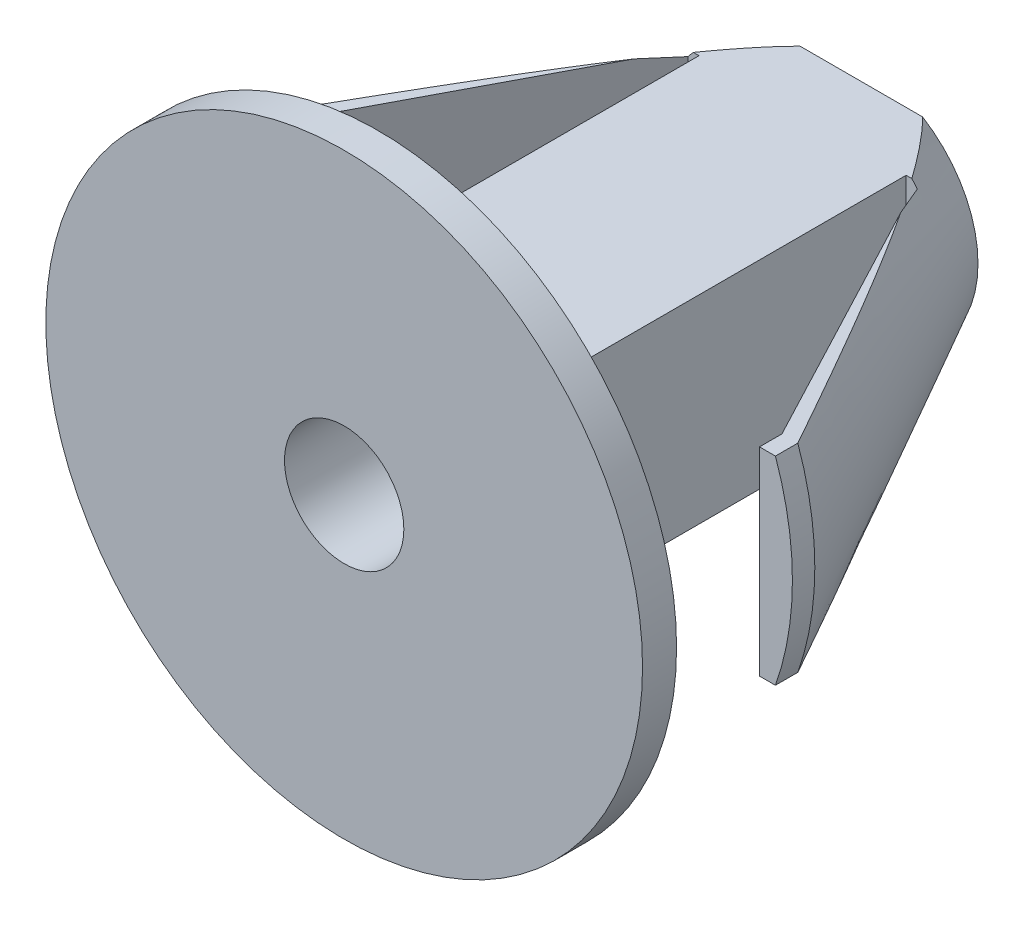
SolidWorks part; units mm, degrees
ref_plane "Front Plane" through (0, 0, 0) normal (0, 0, 1) x (1, 0, 0)
ref_plane "Top Plane" through (0, 0, 0) normal (0, 1, 0) x (1, 0, 0)
ref_plane "Right Plane" through (0, 0, 0) normal (1, 0, 0) x (0, 0, -1)
sketch "Sketch2" plane through (0, 0, 0) normal (0, 1, 0) x (1, 0, 0)
  line L0 (0, 5.1698) -> (-2.9321, 5.1698)
  line L1 (-2.9321, 5.1698) -> (-7.5, -3.4997)
  line L2 (-7.5, -3.4997) -> (-7.5, -7.8302)
  line L3 (-7.5, -7.8302) -> (0, -7.8302)
  line L4 (0, -7.8302) -> (0, 5.1698)
  dimension "D1" = 7.5
  dimension "D2" = 13
revolve "Revolve1" add sketch "Sketch2" angle 360 about L4
sketch "Sketch3" plane through (0, 0, 0) normal (0, 1, 0) x (1, 0, 0)
  line L0 (-7.6964, -4.0631) -> (-4.4271, -4.0631)
  line L1 (-4.4271, -4.0631) -> (-4.4271, -6.9748)
  line L2 (-4.4271, -6.9748) -> (-8.4456, -6.9748)
  line L3 (-8.4456, -6.9748) -> (-7.6964, -4.0631)
  line L4 (0, 0) -> (0, -8.4221) construction
  line L5 (8.4456, -6.9748) -> (7.6964, -4.0631)
  line L6 (4.4271, -6.9748) -> (8.4456, -6.9748)
  line L7 (4.4271, -4.0631) -> (4.4271, -6.9748)
  line L8 (7.6964, -4.0631) -> (4.4271, -4.0631)
extrude "Cut-Extrude1" cut sketch "Sketch3" against normal through all both and the other way through all
sketch "Sketch4" plane through (0, 0, 0) normal (0, 1, 0) x (1, 0, 0)
  line L0 (-6.673, -4.0631) -> (-6.673, -3.4997)
  line L1 (-7.5, -4.0631) -> (-4.4271, -4.0631) construction
  line L2 (7.5, -3.4997) -> (-7.5, -3.4997) construction
  line L3 (-6.673, -3.4997) -> (-2.8837, 3.6921)
  line L4 (-2.6031, 3.6921) -> (-2.6031, -4.0631)
  line L6 (-2.9321, 5.1698) -> (-7.5, -3.4997) construction
  line L7 (-2.8837, 3.6921) -> (-2.6031, 3.6921)
  line L8 (0, 5.6234) -> (0, -0.5002) construction
  line L14 (-6.673, -4.0631) -> (-6.673, -6.9748)
  line L15 (-4.4271, -6.9748) -> (-7.5, -6.9748) construction
  line L16 (-6.673, -6.9748) -> (-2.6031, -6.9748)
  line L17 (-2.6031, -6.9748) -> (-2.6031, -4.0631)
  line L18 (2.6031, -6.9748) -> (2.6031, -4.0631)
  line L19 (6.673, -6.9748) -> (2.6031, -6.9748)
  line L20 (6.673, -4.0631) -> (6.673, -6.9748)
  line L21 (2.8837, 3.6921) -> (2.6031, 3.6921)
  line L22 (2.6031, 3.6921) -> (2.6031, -4.0631)
  line L23 (6.673, -3.4997) -> (2.8837, 3.6921)
  line L24 (6.673, -4.0631) -> (6.673, -3.4997)
extrude "Cut-Extrude3" cut sketch "Sketch4" against normal through all both and the other way through all
sketch "Sketch5" plane through (0, 0, 0) normal (1, 0, 0) x (0, 0, -1)
  line L0 (-6.9748, 2.4952) -> (8.753, 2.4952)
  line L1 (-6.9748, -7.0338) -> (-6.9748, 7.0338) construction
  line L2 (8.753, 2.4952) -> (-4.2275, 9.0244)
  line L3 (-4.2275, 9.0244) -> (-6.9748, 9.0244)
  line L4 (-6.9748, 9.0244) -> (-6.9748, 2.4952)
  line L5 (0, 0) -> (7.759, 0) construction
  line L6 (-6.9748, -9.0244) -> (-6.9748, -2.4952)
  line L7 (-4.2275, -9.0244) -> (-6.9748, -9.0244)
  line L8 (8.753, -2.4952) -> (-4.2275, -9.0244)
  line L9 (-6.9748, -2.4952) -> (8.753, -2.4952)
extrude "Cut-Extrude4" cut sketch "Sketch5" against normal through all both and the other way through all
sketch "Sketch6" plane through (0, 0, 0) normal (0, 0, 1) x (1, 0, 0)
  line L0 (-7.6034, 0) -> (6.2084, 0) construction
  line L1 (0, 2.0728) -> (0, -2.9962) construction
  circle A0 centre (0, 0) radius 1.5
extrude "Cut-Extrude5" cut sketch "Sketch6" against normal through all both and the other way through all
sketch "Sketch8" plane through (0, 0, -5.1698) normal (0, 0, -1) x (-1, 0, 0)
  circle A0 centre (0, 0) radius 2.2645
extrude "Cut-Extrude6" cut sketch "Sketch8" against normal blind 3
